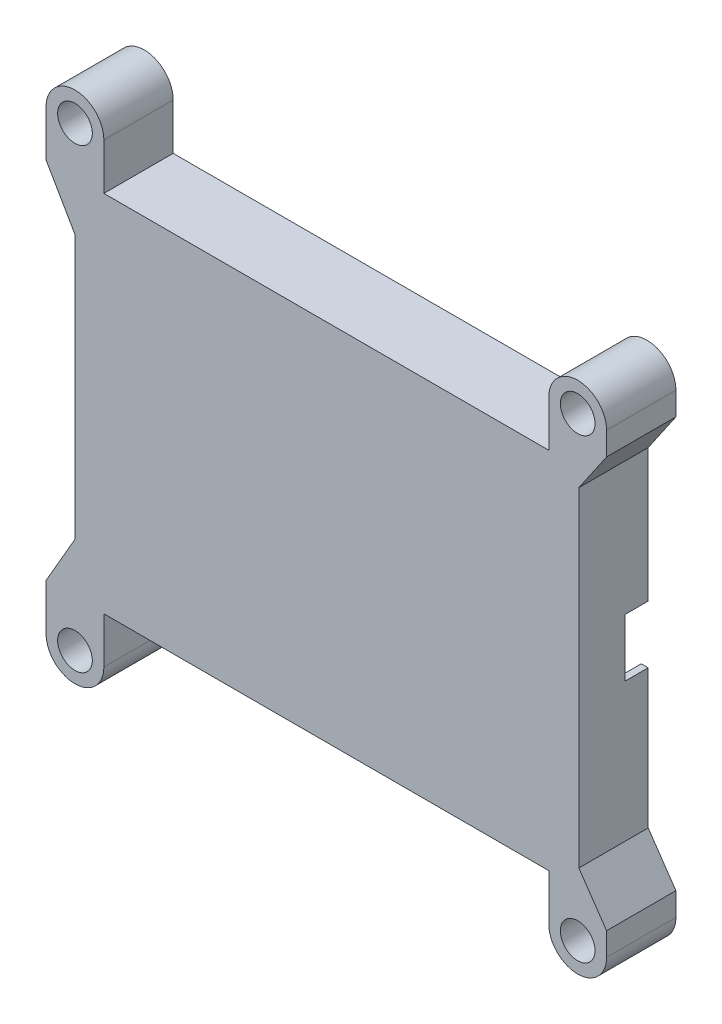
SolidWorks part; units mm, degrees
ref_plane "Front" through (0, 0, 0) normal (0, 0, 1) x (1, 0, 0)
ref_plane "Top" through (0, 0, 0) normal (0, 1, 0) x (1, 0, 0)
ref_plane "Right" through (0, 0, 0) normal (1, 0, 0) x (0, 0, -1)
sketch "草图1" plane through (0, 0, 0) normal (0, 0, 1) x (1, 0, 0)
  line L0 (0, 55.4124) -> (0, -66.1187) construction
  line L1 (-87.3866, 0) -> (75.5228, 0) construction
  line L2 (-46, 22.842) -> (-46, -22.842)
  line L3 (-46, -22.842) -> (-51, -31.5022)
  line L4 (-51, -31.5022) -> (-51, -39.5022)
  line L5 (-41, -39.5022) -> (-41, -31.5022)
  line L6 (-41, -31.5022) -> (36, -31.5022)
  line L7 (46, 39.5022) -> (46, -39.5022)
  line L8 (36, 39.5022) -> (36, 31.5022)
  line L9 (36, -31.5022) -> (36, -39.5022)
  line L10 (36, 31.5022) -> (-41, 31.5022)
  line L11 (-46, 22.842) -> (-51, 31.5022)
  line L12 (-51, 31.5022) -> (-51, 39.5022)
  line L13 (-41, 39.5022) -> (-41, 31.5022)
  line L19 (25, 13.5) -> (-25, -13.5) construction
  line L20 (25, -13.5) -> (-25, 13.5) construction
  arc A0 (-51, -39.5022) -> (-41, -39.5022) centre (-46, -39.5022) ccw
  arc A1 (36, -39.5022) -> (46, -39.5022) centre (41, -39.5022) ccw
  arc A2 (46, 39.5022) -> (36, 39.5022) centre (41, 39.5022) ccw
  arc A3 (-51, 39.5022) -> (-41, 39.5022) centre (-46, 39.5022) cw
  point P25 (0, 0)
  dimension "D3" = 5
  dimension "D5" = 5
  dimension "D9" = 5
  dimension "D12" = 5
  dimension "D2" = 92
  dimension "D4" = 8
  dimension "D6" = 8
  dimension "D7" = 30
  dimension "D8" = 5
  dimension "D10" = 8
  dimension "D11" = 63.0044
  dimension "D13" = 8
  dimension "D14" = 5
  dimension "D15" = 30
  dimension "D16" = 27
  dimension "D17" = 50
extrude "凸台-拉伸1" add sketch "草图1" along normal blind 2
sketch "草图2" plane through (0, 0, 0) normal (0, 0, -1) x (-1, 0, 0)
  line L0 (-46, -39.5022) -> (-46, 39.5022) construction
  line L1 (-40, -13.5) -> (10, -13.5)
  line L2 (-40, -13.5) -> (-40, 13.5)
  line L3 (-40, 13.5) -> (10, 13.5)
  line L4 (10, -13.5) -> (10, 13.5)
  point P0 (0, 0)
  line M3 (46, 22.842) -> (51, 31.5022)
  line M4 (51, 31.5022) -> (51, 39.5022)
  arc M5 (51, 39.5022) -> (41, 39.5022) centre (46, 39.5022) ccw
  line M6 (41, 39.5022) -> (41, 31.5022)
  line M7 (41, 31.5022) -> (-36, 31.5022)
  line M8 (-36, 31.5022) -> (-36, 39.5022)
  arc M9 (-36, 39.5022) -> (-46, 39.5022) centre (-41, 39.5022) ccw
  line M10 (-46, 39.5022) -> (-46, -39.5022)
  arc M11 (-46, -39.5022) -> (-36, -39.5022) centre (-41, -39.5022) ccw
  line M12 (-36, -39.5022) -> (-36, -31.5022)
  line M13 (-36, -31.5022) -> (41, -31.5022)
  line M14 (41, -31.5022) -> (41, -39.5022)
  arc M15 (41, -39.5022) -> (51, -39.5022) centre (46, -39.5022) ccw
  line M16 (51, -39.5022) -> (51, -31.5022)
  line M17 (51, -31.5022) -> (46, -22.842)
  line M18 (46, -22.842) -> (46, 22.842)
  dimension "D1" = 27
  dimension "D2" = 50
  dimension "D3" = 6
extrude "凸台-拉伸2" add sketch "草图2" along normal blind 10 contours L4 L1 L2 L3 M18 M3 M4 M5 M6 M7 M8 M9 M10 M11 M12 M13 M14 M15 M16 M17
sketch "草图3" plane through (0, 0, -10) normal (0, 0, -1) x (-1, 0, 0)
  circle A0 centre (-41, 39.5022) radius 3
  circle A1 centre (46, -39.5022) radius 3
  circle A2 centre (46, 39.5022) radius 3
  circle A3 centre (-41, -39.5022) radius 3
  dimension "D1" = 6
  dimension "D2" = 6
  dimension "D3" = 6
  dimension "D4" = 6
extrude "切除-拉伸1" cut sketch "草图3" against normal through all
sketch "草图5" plane through (0, 0, 0) normal (0, 0, -1) x (-1, 0, 0)
  line L0 (-40, -13.5) -> (-40, 13.5) construction
  line L1 (-38.8, 11.75) -> (8.2, 11.75)
  line L2 (-38.8, 11.75) -> (-38.8, 10.15)
  line L3 (-38.8, 10.15) -> (8.2, 10.15)
  line L4 (8.2, 11.75) -> (8.2, 10.15)
  line L5 (-38.8, -11.75) -> (8.2, -11.75)
  line L6 (-38.8, -11.75) -> (-38.8, -10.15)
  line L7 (-38.8, -10.15) -> (8.2, -10.15)
  line L8 (8.2, -11.75) -> (8.2, -10.15)
  line L9 (-40, -13.5) -> (10, -13.5) construction
  line L10 (-40, 13.5) -> (10, 13.5) construction
  dimension "D1" = 47
  dimension "D2" = 47
  dimension "D3" = 1.6
  dimension "D4" = 1.6
  dimension "D5" = 1.2
  dimension "D6" = 1.2
  dimension "D7" = 1.75
  dimension "D8" = 1.75
extrude "切除-拉伸2" cut sketch "草图5" against normal blind 1.6
sketch "草图6" plane through (40, 0, 0) normal (-1, 0, 0) x (0, 0, 1)
  line L0 (-10, -4.5) -> (-10, 5.5)
  line L1 (-10, -4.5) -> (-6, -4.5)
  line L2 (-10, 5.5) -> (-6, 5.5)
  line L3 (-6, -4.5) -> (-6, 5.5)
  line L4 (-10, -13.5) -> (-10, 13.5) construction
  line L7 (-10, 13.5) -> (0, 13.5) construction
  dimension "D1" = 4
  dimension "D2" = 10
  dimension "D3" = 18
extrude "切除-拉伸3" cut sketch "草图6" against normal through all
sketch "草图7" plane through (0, 0, -10) normal (0, 0, -1) x (-1, 0, 0)
  line L0 (44, -29.5022) -> (-36, -29.5022)
  line L1 (-36, -29.5022) -> (-36, -15.5)
  line L2 (-36, -15.5) -> (44, -15.5)
  line L3 (44, -15.5) -> (44, 29.5022)
  line L4 (44, 29.5022) -> (-36, 29.5022)
  line L5 (-36, 29.5022) -> (-36, 15.5)
  line L6 (-36, 15.5) -> (12, 15.5)
  line L7 (12, 15.5) -> (12, -15.5)
  line L8 (44, -29.5022) -> (44, -15.5)
  line L9 (-36, -31.5022) -> (41, -31.5022) construction
  line L10 (-40, -13.5) -> (10, -13.5) construction
  line L11 (10, -13.5) -> (10, 13.5) construction
  line L12 (46, -22.842) -> (46, 22.842) construction
  line L13 (-40, 13.5) -> (10, 13.5) construction
  line L15 (41, 31.5022) -> (-36, 31.5022) construction
  line L17 (-46, -4.5) -> (-46, -39.5022) construction
  line L18 (-46, 39.5022) -> (-46, 5.5) construction
  dimension "D1" = 10
  dimension "D2" = 10
  dimension "D3" = 2
  dimension "D4" = 2
  dimension "D5" = 2
  dimension "D6" = 2
  dimension "D7" = 2
  dimension "D8" = 2
extrude "切除-拉伸4" cut sketch "草图7" against normal blind 10 contours L0 L8 L2 L1 | L6 L7 L2 L3 L4 L5
sketch "草图9" plane through (0, 0, -10) normal (0, 0, -1) x (-1, 0, 0)
  line L0 (-46, -35.5022) -> (-41.2, -28.5022)
  line L1 (-46, -4.5) -> (-46, -39.5022) construction
  line L2 (-41.2, -28.5022) -> (-41.2, 28.5022)
  line L3 (-41.2, 28.5022) -> (-46, 35.5022)
  line L4 (-46, 39.5022) -> (-46, 5.5) construction
  line L5 (-46, 35.5022) -> (-46, -35.5022)
  arc A0 (-36, 39.5022) -> (-46, 39.5022) centre (-41, 39.5022) ccw construction
  arc A1 (-46, -39.5022) -> (-36, -39.5022) centre (-41, -39.5022) ccw construction
  dimension "D1" = 1.2
  dimension "D2" = 7
  dimension "D3" = 7
  dimension "D4" = 4
  dimension "D5" = 4
extrude "切除-拉伸5" cut sketch "草图9" against normal up to next
